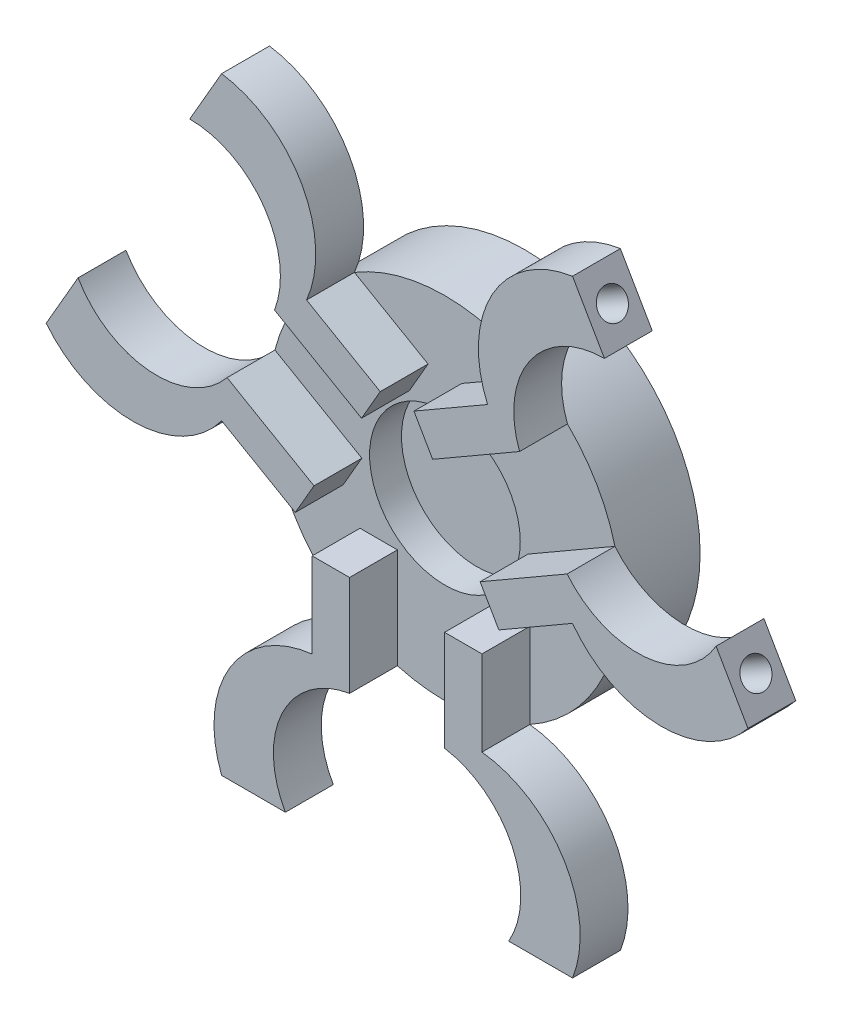
SolidWorks part; units mm, degrees
ref_plane "前视基准面" through (0, 0, 0) normal (0, 0, 1) x (1, 0, 0)
ref_plane "上视基准面" through (0, 0, 0) normal (0, 1, 0) x (1, 0, 0)
ref_plane "右视基准面" through (0, 0, 0) normal (1, 0, 0) x (0, 0, -1)
other "Configuration Table"
sketch "草图1" plane through (0, 0, 0) normal (0, 0, 1) x (1, 0, 0)
  circle A0 centre (0, 0) radius 11
  dimension "D1" = 22
extrude "凸台-拉伸1" add sketch "草图1" along normal blind 2
sketch "草图2" plane through (0, 0, 2) normal (0, 0, 1) x (1, 0, 0)
  line L8 (-11, -19.0526) -> (-7, -19.0526)
  line L9 (22, 0) -> (11, 19.0526)
  line L10 (11, 19.0526) -> (-11, 19.0526)
  line L11 (-11, 19.0526) -> (-22, 0)
  line L12 (-22, 0) -> (-11, -19.0526)
  line L13 (-11, -19.0526) -> (11, -19.0526)
  line L14 (11, -19.0526) -> (22, 0)
  line L15 (-5.3238, -9.6259) -> (-5.3238, -4.2939)
  line L16 (-5.3238, -4.2939) -> (-2.9782, -4.2939)
  line L17 (-2.9782, -4.2939) -> (-2.9782, -10.5892)
  line L18 (0, 0) -> (0, -19.0526) construction
  line L19 (11, -19.0526) -> (7, -19.0526)
  line L20 (5.3238, -9.6259) -> (5.3238, -4.2939)
  line L21 (5.3238, -4.2939) -> (2.9782, -4.2939)
  line L22 (2.9782, -4.2939) -> (2.9782, -10.5892)
  line L23 (-1.0567, 6.7575) -> (-2.2295, 4.7262)
  line L24 (-2.2295, 4.7262) -> (-7.6814, 7.8738)
  line L25 (-5.6743, 9.4235) -> (-1.0567, 6.7575)
  line L26 (-6.3805, -2.4636) -> (-5.2077, -0.4322)
  line L27 (-5.2077, -0.4322) -> (-10.6596, 2.7154)
  line L28 (-10.9981, 0.2024) -> (-6.3805, -2.4636)
  line L29 (-11, 19.0526) -> (-22, 0)
  line L30 (6.3805, -2.4636) -> (5.2077, -0.4322)
  line L31 (5.2077, -0.4322) -> (10.6596, 2.7154)
  line L32 (10.9981, 0.2024) -> (6.3805, -2.4636)
  line L33 (1.0567, 6.7575) -> (2.2295, 4.7262)
  line L34 (2.2295, 4.7262) -> (7.6814, 7.8738)
  line L35 (5.6743, 9.4235) -> (1.0567, 6.7575)
  line L36 (22, 0) -> (11, 19.0526)
  arc A0 (-11, -19.0526) -> (-5.3238, -9.6259) centre (-4.5393, -16.5205) cw
  circle A4 centre (0, 0) radius 19.0526 construction
  circle A5 centre (0, 0) radius 11 construction
  arc A6 (-7, -19.0526) -> (-2.9782, -10.5892) centre (-2.0509, -16.2171) cw
  arc A7 (7, -19.0526) -> (2.9782, -10.5892) centre (2.0509, -16.2171) ccw
  arc A8 (11, -19.0526) -> (5.3238, -9.6259) centre (4.5393, -16.5205) ccw
  arc A9 (-11, 19.0526) -> (-5.6743, 9.4235) centre (-12.0375, 12.1914) cw
  arc A10 (-13, 15.5885) -> (-7.6814, 7.8738) centre (-13.0189, 9.8847) cw
  arc A11 (-22, 0) -> (-10.9981, 0.2024) centre (-16.5768, 4.3291) ccw
  arc A12 (-20, 3.4641) -> (-10.6596, 2.7154) centre (-15.0699, 6.3324) ccw
  arc A13 (22, 0) -> (10.9981, 0.2024) centre (16.5768, 4.3291) cw
  arc A14 (20, 3.4641) -> (10.6596, 2.7154) centre (15.0699, 6.3324) cw
  arc A15 (11, 19.0526) -> (5.6743, 9.4235) centre (12.0375, 12.1914) ccw
  arc A16 (13, 15.5885) -> (7.6814, 7.8738) centre (13.0189, 9.8847) ccw
  point P61 (0, 0)
  circle M2 centre (0, 0) radius 11
  dimension "D1" = 4
  dimension "D2" = 3
  dimension "D3" = 22
extrude "凸台-拉伸2" add sketch "草图2" along normal blind 3 contours L25 L24 L23 M2 | L11 A10 A9 M2 | A12 L11 A11 M2 | L28 L26 L27 M2 | L8 A6 A0 M2 | L17 L16 L15 M2 | L21 L22 L20 M2 | L13 A8 A7 M2 | L9 A14 A13 M2 | L32 L31 L30 M2 | L35 L33 L34 M2 | A16 L9 A15 M2
sketch "草图4" plane through (-16.5, 9.5263, 0) normal (-0.866, 0.5, 0) x (0, 0, 1)
  circle A0 centre (3.5, 9) radius 0.9
  circle A1 centre (3.5, -9) radius 0.9
  dimension "D1" = 1.8
  dimension "D2" = 1.8
extrude "切除-拉伸1" cut sketch "草图4" against normal blind 4
sketch "草图5" plane through (16.5, 9.5263, 0) normal (0.866, 0.5, 0) x (0, 0, -1)
  circle A0 centre (-3.5, -9) radius 0.9
  circle A1 centre (-3.5, 9) radius 0.9
  dimension "D1" = 1.8
  dimension "D2" = 1.8
extrude "切除-拉伸2" cut sketch "草图5" against normal blind 4
sketch "草图6" plane through (0, -19.0526, 0) normal (0, -1, 0) x (1, 0, 0)
  circle A0 centre (-9, 3.5) radius 0.9
  circle A1 centre (9, 3.5) radius 0.9
  dimension "D1" = 1.8
  dimension "D2" = 1.8
extrude "切除-拉伸3" cut sketch "草图6" against normal blind 4
sketch "草图8" plane through (0, 0, 0) normal (0, 0, -1) x (-1, 0, 0)
  circle A1 centre (0, 0) radius 11
  circle A2 centre (0, 0) radius 11
  dimension "D1" = 0
extrude "凸台-拉伸3" add sketch "草图8" along normal blind 3
sketch "草图9" plane through (0, 0, 2) normal (0, 0, 1) x (1, 0, 0)
  circle A0 centre (0, 0) radius 4.7235
extrude "切除-拉伸4" cut sketch "草图9" against normal blind 2
